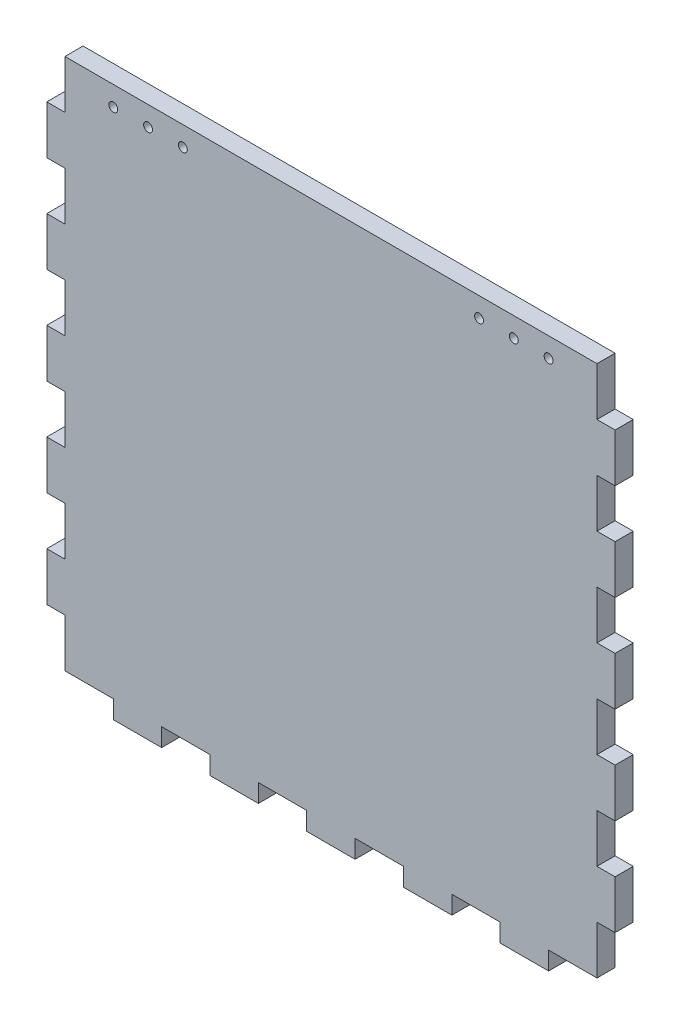
SolidWorks part; units mm, degrees
ref_plane "Front Plane" through (0, 0, 0) normal (0, 0, 1) x (1, 0, 0)
ref_plane "Top Plane" through (0, 0, 0) normal (0, 1, 0) x (1, 0, 0)
ref_plane "Right Plane" through (0, 0, 0) normal (1, 0, 0) x (0, 0, -1)
sketch "Sketch2" plane through (0, 0, 0) normal (0, 0, 1) x (1, 0, 0)
  line L1 (-139.7, -139.7) -> (139.7, -139.7)
  line L2 (-139.7, -139.7) -> (-139.7, 139.7)
  line L3 (-139.7, 139.7) -> (139.7, 139.7)
  line L4 (139.7, -139.7) -> (139.7, 139.7)
  line L5 (-139.7, -139.7) -> (139.7, 139.7) construction
  line L6 (-139.7, 139.7) -> (139.7, -139.7) construction
  point P0 (0, 0)
  dimension "D1" = 279.4
  dimension "D2" = 279.4
extrude "Boss-Extrude1" add sketch "Sketch2" along normal blind 9.525
sketch "Sketch3" plane through (0, 139.7, 0) normal (0, 1, 0) x (1, 0, 0)
  line L0 (-158.9087, 0) -> (158.9087, 0) construction
  line L1 (-114.3, -9.525) -> (-88.9, -9.525)
  line L2 (-114.3, -9.525) -> (-114.3, 0)
  line L3 (-114.3, 0) -> (-88.9, 0)
  line L4 (-88.9, -9.525) -> (-88.9, 0)
  line L6 (-139.7, -9.525) -> (-139.7, 0) construction
  dimension "D1" = 25.4
  dimension "D2" = 25.4
sketch "Sketch4" plane through (139.7, 0, 0) normal (1, 0, 0) x (0, 0, -1)
  line L0 (0, 158.9087) -> (0, -158.9087) construction
  line L1 (0, -114.3) -> (-9.525, -114.3)
  line L2 (0, -114.3) -> (0, -88.9)
  line L3 (0, -88.9) -> (-9.525, -88.9)
  line L4 (-9.525, -114.3) -> (-9.525, -88.9)
  line L5 (-9.525, -139.7) -> (-9.525, 139.7) construction
  line L7 (-9.525, -139.7) -> (0, -139.7) construction
  dimension "D1" = 25.4
  dimension "D2" = 25.4
extrude "Boss-Extrude3" add sketch "Sketch4" along normal blind 9.525
pattern_linear "LPattern2" count 5 spacing 50.8 along (0, 1, 0) of "Boss-Extrude3"
mirror "Mirror2" about plane through (0, 0, 0) normal (1, 0, 0) of "LPattern2", "Boss-Extrude3"
sketch "Sketch5" plane through (0, -139.7, 0) normal (0, -1, 0) x (1, 0, 0)
  line L1 (-114.3, 9.525) -> (-88.9, 9.525)
  line L2 (-114.3, 9.525) -> (-114.3, 0)
  line L3 (-114.3, 0) -> (-88.9, 0)
  line L4 (-88.9, 9.525) -> (-88.9, 0)
extrude "Boss-Extrude4" add sketch "Sketch5" along normal blind 9.525
pattern_linear "LPattern3" count 5 spacing 50.8 along (1, 0, 0) of "Boss-Extrude4"
sketch "Sketch6" plane through (0, 0, 9.525) normal (0, 0, 1) x (1, 0, 0)
  line L0 (139.7, 139.7) -> (-139.7, 139.7) construction
  line L1 (77.7748, 139.7) -> (114.3, 139.7) construction
  line L2 (77.7748, 139.7) -> (77.7748, 129.3876) construction
  line L3 (77.7748, 129.3876) -> (114.3, 129.3876) construction
  line L4 (114.3, 139.7) -> (114.3, 129.3876) construction
  line L5 (77.7748, 139.7) -> (114.3, 129.3876) construction
  line L6 (77.7748, 129.3876) -> (114.3, 139.7) construction
  line L7 (139.7, 114.3) -> (139.7, 139.7) construction
  circle A0 centre (114.3, 129.3876) radius 2.3368
  circle A1 centre (77.7748, 129.3876) radius 2.3368
  circle A2 centre (96.0374, 129.3876) radius 2.3368
  point P4 (96.0374, 134.5438)
  point P7 (114.3, 134.5438)
  dimension "D4" = 4.6736
  dimension "D5" = 4.6736
  dimension "D6" = 4.6736
  dimension "D1" = 36.5252
  dimension "D2" = 10.3124
  dimension "D3" = 25.4
extrude "Cut-Extrude1" cut sketch "Sketch6" against normal through all
mirror "Mirror3" about plane through (0, 0, 0) normal (1, 0, 0) of "Cut-Extrude1"
